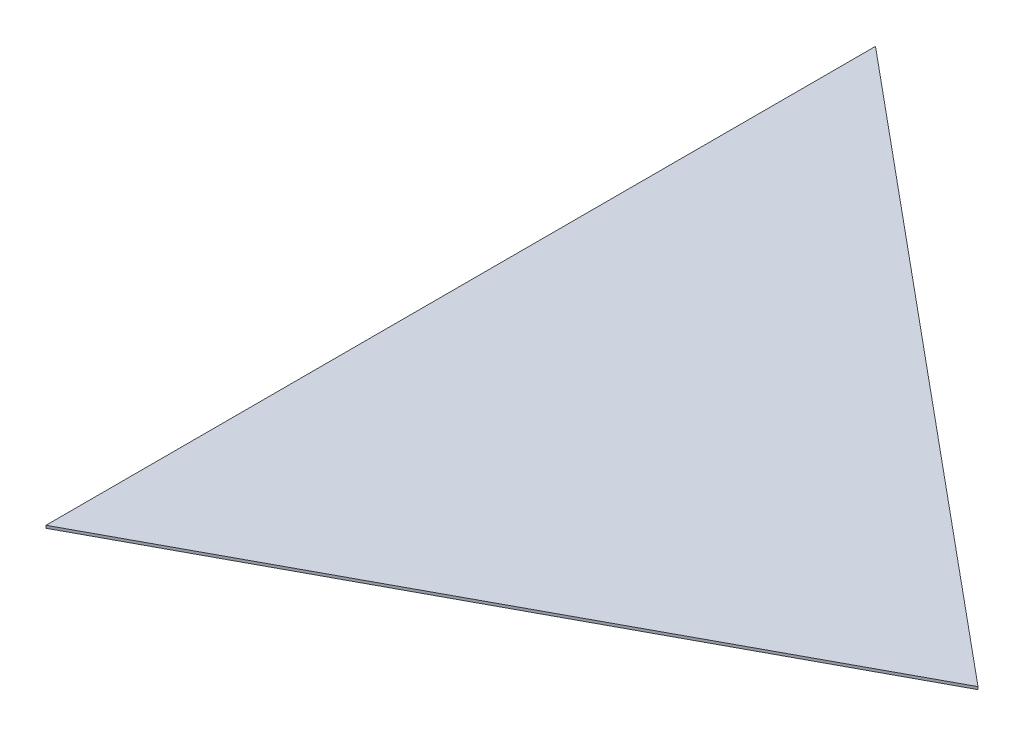
SolidWorks part; units mm, degrees
ref_plane "Front Plane" through (0, 0, 0) normal (0, 0, 1) x (1, 0, 0)
ref_plane "Top Plane" through (0, 0, 0) normal (0, 1, 0) x (1, 0, 0)
ref_plane "Right Plane" through (0, 0, 0) normal (1, 0, 0) x (0, 0, -1)
sketch "Sketch1" plane through (0, 0, 0) normal (0, 1, 0) x (1, 0, 0)
  line L0 (0, 0) -> (0, 501.904)
  line L1 (0, 501.904) -> (366.522, 197.4082)
  line L2 (366.522, 197.4082) -> (0, 0)
  dimension "D1" = 501.904
  dimension "D2" = 476.504
  dimension "D3" = 366.522
extrude "Boss-Extrude1" add sketch "Sketch1" along normal blind 1.5875
